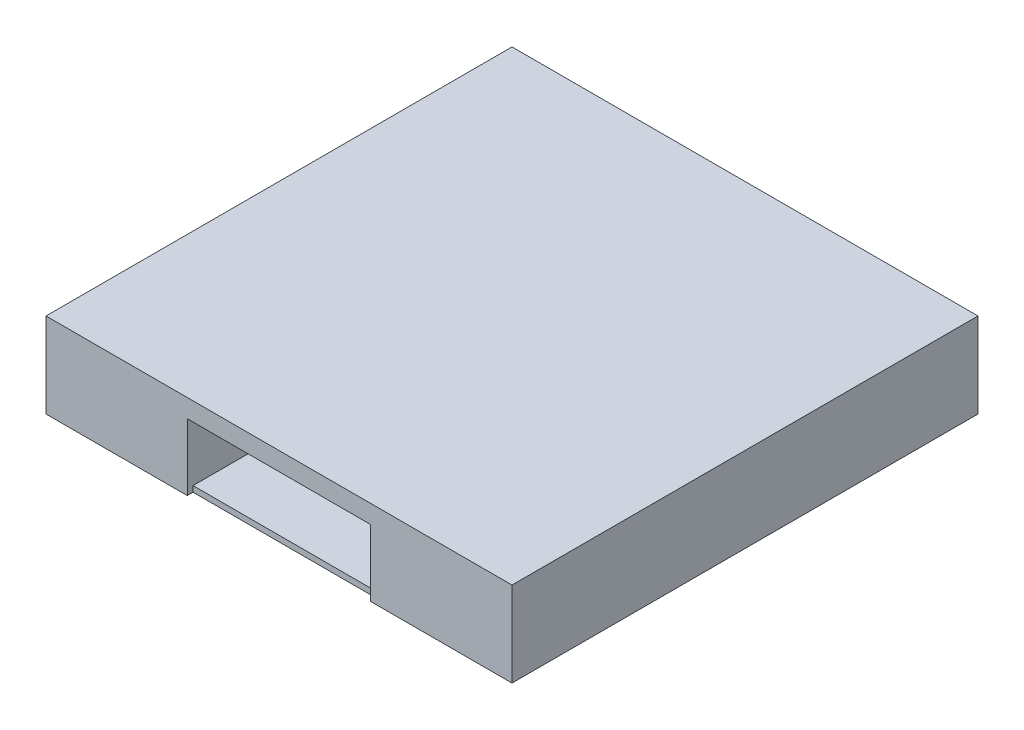
SolidWorks part; units mm, degrees
ref_plane "Front Plane" through (0, 0, 0) normal (0, 0, 1) x (1, 0, 0)
ref_plane "Top Plane" through (0, 0, 0) normal (0, 1, 0) x (1, 0, 0)
ref_plane "Right Plane" through (0, 0, 0) normal (1, 0, 0) x (0, 0, -1)
sketch "Sketch3" plane through (0, 0, 0) normal (0, 1, 0) x (1, 0, 0)
  line L0 (0, 0) -> (0, 508)
  line L1 (0, 508) -> (508, 508)
  line L2 (508, 508) -> (508, 0)
  line L3 (508, 0) -> (0, 0)
  dimension "D1" = 508
  dimension "D2" = 508
extrude "Boss-Extrude1" add sketch "Sketch3" along normal blind 6.3
sketch "Sketch4" plane through (0, 6.3, 0) normal (0, 1, 0) x (1, 0, 0)
  line L11 (0, 508) -> (508, 508)
  line L12 (0, 508) -> (0, 0)
  line L13 (0, 0) -> (508, 0)
  line L14 (6.3, 6.3) -> (501.7, 6.3)
  line L15 (501.7, 6.3) -> (501.7, 501.7)
  line L16 (6.3, 501.7) -> (6.3, 6.3)
  line L17 (501.7, 501.7) -> (6.3, 501.7)
  line L18 (6.3, 6.3) -> (501.7, 6.3)
  line L19 (501.7, 6.3) -> (501.7, 501.7)
  line L20 (6.3, 501.7) -> (6.3, 6.3)
  line L21 (501.7, 501.7) -> (6.3, 501.7)
  line L22 (508, 508) -> (508, 0)
  dimension "D1" = 6.3
extrude "Boss-Extrude2" add sketch "Sketch4" along normal blind 80
sketch "Sketch5" plane through (0, 86.3, 0) normal (0, 1, 0) x (1, 0, 0)
  line L1 (0, 508) -> (508, 508)
  line L2 (0, 508) -> (0, 0)
  line L3 (0, 0) -> (508, 0)
  line L4 (508, 508) -> (508, 0)
extrude "Boss-Extrude3" add sketch "Sketch5" along normal blind 6.3
sketch "Sketch6" plane through (0, 0, 0) normal (0, 0, 1) x (1, 0, 0)
  line L1 (154, 72.6) -> (354, 72.6)
  line L2 (154, 72.6) -> (154, 0)
  line L3 (0, 0) -> (508, 0) construction
  line L4 (354, 72.6) -> (354, 0)
  line L5 (0, 92.6) -> (508, 92.6) construction
  point P6 (254, 72.6)
  point P9 (254, 92.6)
  dimension "D1" = 200
  dimension "D2" = 20
extrude "Cut-Extrude2" cut sketch "Sketch6" against normal blind 6.3 and the other way through all
sketch "Sketch7" plane through (0, 0, 0) normal (0, 0, 1) x (1, 0, 0)
  line L0 (0, 92.6) -> (0, 0)
sketch "Sketch8" plane through (0, 0, 0) normal (0, 0, 1) x (1, 0, 0)
  line L0 (0, 92.6) -> (508, 92.6) construction
  line L1 (154, 0) -> (147.7, 0)
  line L2 (154, 0) -> (154, 92.6)
  line L3 (154, 92.6) -> (147.7, 92.6)
  line L4 (147.7, 0) -> (147.7, 92.6)
  line L5 (354, 0) -> (508, 0) construction
  line L6 (354, 92.6) -> (360.3, 92.6)
  line L7 (354, 92.6) -> (354, 0)
  line L8 (354, 0) -> (360.3, 0)
  line L9 (360.3, 92.6) -> (360.3, 0)
  dimension "D1" = 6.3
extrude "Boss-Extrude4" add sketch "Sketch8" against normal blind 508
